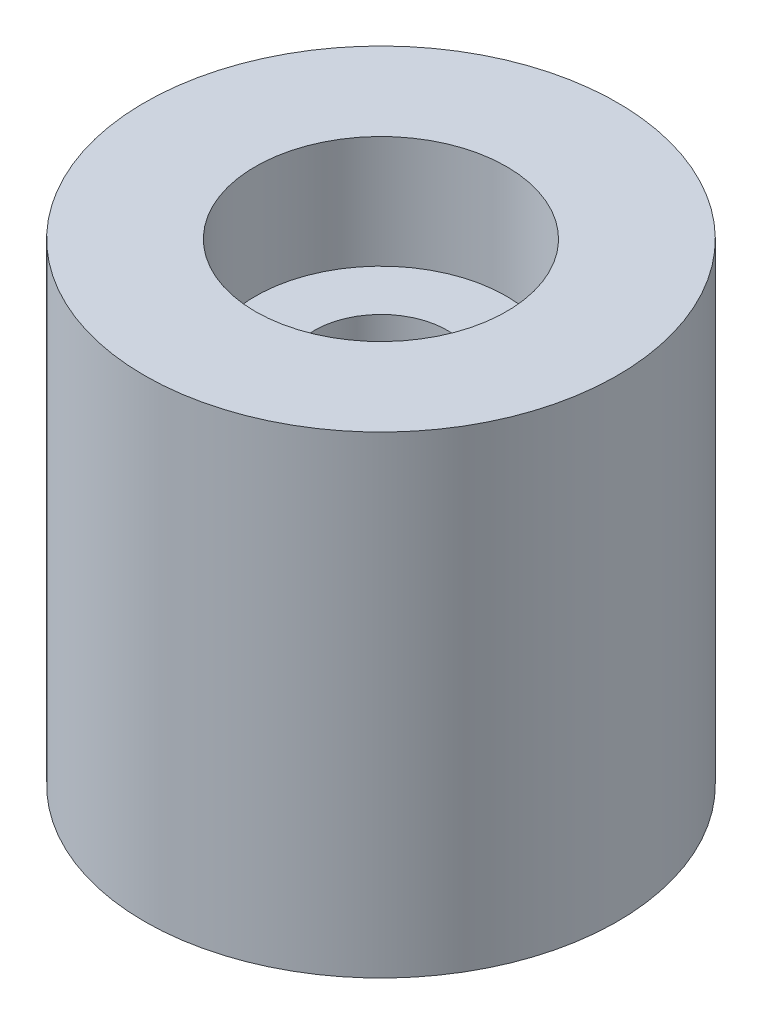
SolidWorks part; units mm, degrees
ref_plane "Front Plane" through (0, 0, 0) normal (0, 0, 1) x (1, 0, 0)
ref_plane "Top Plane" through (0, 0, 0) normal (0, 1, 0) x (1, 0, 0)
ref_plane "Right Plane" through (0, 0, 0) normal (1, 0, 0) x (0, 0, -1)
sketch "Sketch1" plane through (0, 0, 0) normal (0, 1, 0) x (1, 0, 0)
  circle A0 centre (0, 0) radius 8
  circle A1 centre (0, 0) radius 2.25
  dimension "D1" = 4.5
  dimension "D2" = 16
extrude "Boss-Extrude1" add sketch "Sketch1" along normal blind 16
sketch "Sketch2" plane through (0, 16, 0) normal (0, 1, 0) x (1, 0, 0)
  circle A0 centre (0, 0) radius 4.25
  dimension "D1" = 8.5
extrude "Cut-Extrude1" cut sketch "Sketch2" against normal blind 3.8
